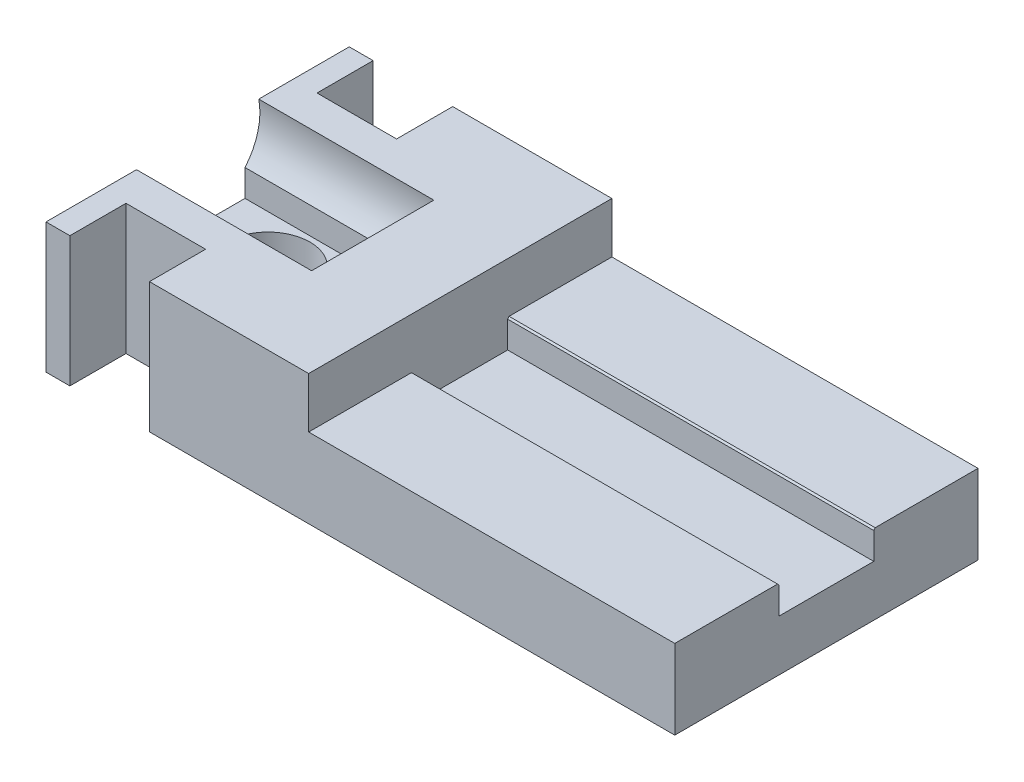
SolidWorks part; units mm, degrees
ref_plane "Front Plane" through (0, 0, 0) normal (0, 0, 1) x (1, 0, 0)
ref_plane "Top Plane" through (0, 0, 0) normal (0, 1, 0) x (1, 0, 0)
ref_plane "Right Plane" through (0, 0, 0) normal (1, 0, 0) x (0, 0, -1)
other "Center of Mass"
sketch "Sketch3" plane through (0, 0, 0) normal (1, 0, 0) x (0, -1, 0)
  point P0 (-14.3071, 0)
  dimension "D1" = 14.3071
sketch "Sketch5" plane through (0, 0, 0) normal (1, 0, 0) x (0, -1, 0)
  line L0 (6.35, 0) -> (-27.0071, 0) construction
  line L1 (6.35, -19.05) -> (-27.0071, -19.05)
  line L2 (6.35, -19.05) -> (6.35, 19.05)
  line L3 (6.35, 19.05) -> (-27.0071, 19.05)
  line L4 (-27.0071, -19.05) -> (-27.0071, 19.05)
  dimension "D1" = 12.7
  dimension "D2" = 38.1
  dimension "D3" = 6.35
extrude "Boss-Extrude2" add sketch "Sketch5" along normal blind 1 and the other way blind 78
sketch "Sketch6" plane through (0, 0, 19.05) normal (0, 0, 1) x (1, 0, 0)
  line L0 (-68, 27.0071) -> (-68, 3.6355)
  line L1 (-68, 3.6355) -> (1, 3.6355)
  line L2 (-78, -6.35) -> (-78, 27.0071) construction
  line L4 (-78, -6.35) -> (1, -6.35)
  line L5 (1, -6.35) -> (1, 27.0071)
  line L6 (1, 27.0071) -> (-78, 27.0071)
  line L7 (-78, 27.0071) -> (-78, -6.35)
  line L9 (1, 3.6355) -> (1, 27.0071)
  line L10 (1, 27.0071) -> (-68, 27.0071)
  dimension "D2" = 10
  dimension "D3" = 3.6355
  dimension "D1" = 0
extrude "Cut-Extrude1" cut sketch "Sketch6" against normal through all
sketch "Sketch7" plane through (0, 0, 0) normal (1, 0, 0) x (0, 0, -1)
  circle A0 centre (0, 8.4965) radius 7.8252
extrude "Cut-Extrude2" cut sketch "Sketch7" against normal through all and the other way through all
sketch "Sketch8" plane through (0, 0, 0) normal (1, 0, 0) x (0, 0, -1)
  line L3 (-6.1323, 3.6355) -> (-19.05, 3.6355)
  line L4 (-19.05, 27.0071) -> (-19.05, 3.6355)
  line L5 (-19.05, 3.6355) -> (-6.1323, 3.6355)
  line L6 (19.05, 3.6355) -> (19.05, 27.0071)
  line L7 (19.05, 27.0071) -> (-19.05, 27.0071)
  line L8 (-19.05, 27.0071) -> (-19.05, 3.6355)
  line L10 (19.05, 3.6355) -> (19.05, 27.0071)
  line L11 (19.05, 27.0071) -> (-19.05, 27.0071)
  line L16 (6.1323, 3.6355) -> (19.05, 3.6355)
  line L17 (6.1323, 3.6355) -> (19.05, 3.6355)
  arc A1 (6.1323, 3.6355) -> (-6.1323, 3.6355) centre (0, 8.4965) ccw
  arc A2 (6.1323, 3.6355) -> (-6.1323, 3.6355) centre (0, 8.4965) ccw
  dimension "D1" = 0
extrude "Cut-Extrude3" cut sketch "Sketch8" against normal through all
sketch "Sketch9" plane through (0, 0, 0) normal (0, 1, 0) x (1, 0, 0)
  line L0 (-78, 19.05) -> (1, 19.05) construction
  line L1 (-78, -19.05) -> (-45, -19.05)
  line L2 (-78, -19.05) -> (-78, 19.05)
  line L3 (-78, 19.05) -> (-45, 19.05)
  line L4 (-45, -19.05) -> (-45, 19.05)
  line L5 (-78, -6.1323) -> (-78, -19.05) construction
  dimension "D1" = 45
extrude "Boss-Extrude6" add sketch "Sketch9" along normal blind 10
sketch "Sketch11" plane through (0, 0, 0) normal (1, 0, 0) x (0, 0, -1)
  circle A0 centre (0, 8.4965) radius 7.8252 construction
  circle A1 centre (0, 8.4965) radius 7.8252
extrude "Cut-Extrude5" cut sketch "Sketch11" against normal through all
sketch "Sketch13" plane through (0, 0, 0) normal (0, 1, 0) x (1, 0, 0)
  line L0 (-65, -37.4) -> (-65, -12)
  line L1 (-65, -12) -> (-75, -12)
  line L2 (-75, -12) -> (-75, -37.4)
  line L3 (-75, -37.4) -> (-65, -37.4)
  line L4 (-11.3614, 0) -> (11.3614, 0) construction
  line L5 (-75, 37.4) -> (-65, 37.4)
  line L6 (-75, 12) -> (-75, 37.4)
  line L7 (-65, 12) -> (-75, 12)
  line L8 (-65, 37.4) -> (-65, 12)
  point P4 (-75, -24.7)
  dimension "D1" = 65
  dimension "D2" = 12
  dimension "D3" = 10
  dimension "D4" = 25.4
extrude "Cut-Extrude6" cut sketch "Sketch13" against normal through all and the other way through all
sketch "Sketch14" plane through (0, 0, 0) normal (1, 0, 0) x (0, 0, -1)
  line L3 (0, 0.0584) -> (0, 40.0584) construction
  line L4 (5.9538, 40.0584) -> (-5.9538, 40.0584)
  line L5 (0, 11.6094) -> (0, -11.6094) construction
  line L6 (-5.9538, 0.0584) -> (-5.9538, 40.0584)
  line L11 (5.9538, 0.0584) -> (5.9538, 40.0584)
  line L13 (-5.9538, 0.0584) -> (5.9538, 0.0584)
  dimension "D2" = 40
extrude "Cut-Extrude8" cut sketch "Sketch14" against normal blind 90 and the other way through all
sketch "Sketch15" plane through (0, 0, 0) normal (0, 1, 0) x (1, 0, 0)
  circle A0 centre (-69.1697, 0) radius 5.2805
extrude "Cut-Extrude9" cut sketch "Sketch15" against normal blind 90 and the other way blind 90
sketch "Sketch16" plane through (-45, 0, 0) normal (1, 0, 0) x (0, 0, -1)
  line L1 (19.05, 10) -> (-19.05, 10)
  line L2 (19.05, 10) -> (19.05, -6.35)
  line L3 (19.05, -6.35) -> (-19.05, -6.35)
  line L4 (-19.05, 10) -> (-19.05, -6.35)
extrude "Boss-Extrude7" add sketch "Sketch16" against normal blind 11
